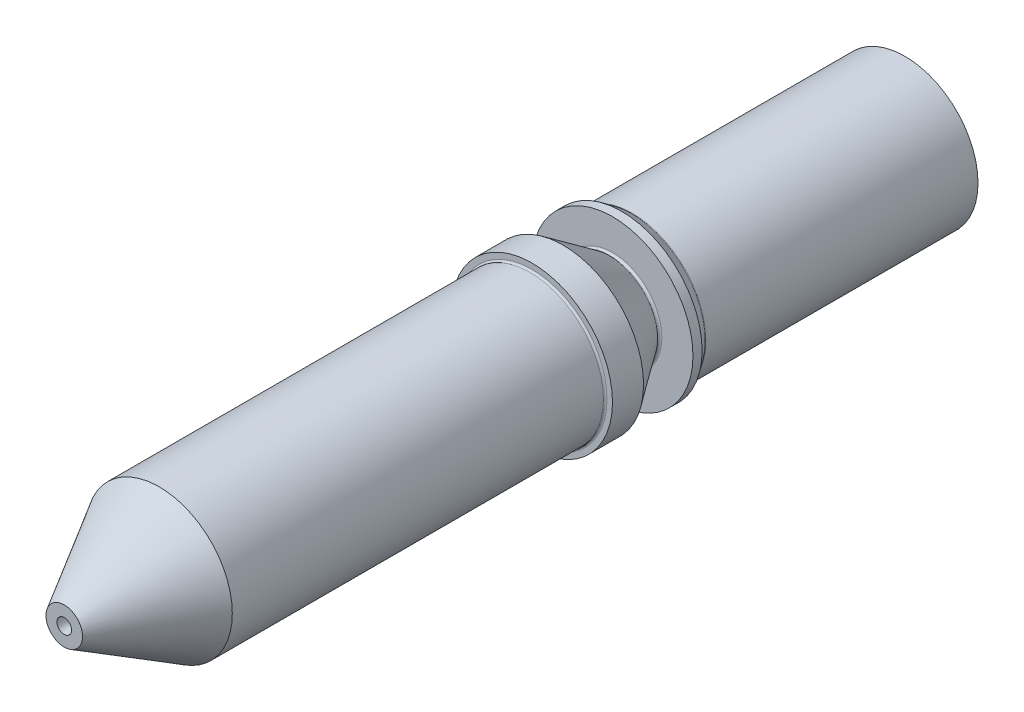
SolidWorks part; units mm, degrees
material "AISI Type 316L stainless steel"
ref_plane "Front Plane" through (0, 0, 0) normal (0, 0, 1) x (1, 0, 0)
ref_plane "Top Plane" through (0, 0, 0) normal (0, 1, 0) x (1, 0, 0)
ref_plane "Right Plane" through (0, 0, 0) normal (1, 0, 0) x (0, 0, -1)
sketch "Sketch1" plane through (0, 0, 0) normal (0, 1, 0) x (1, 0, 0)
  line L0 (0.5, -23) -> (2, -20.4019)
  line L1 (2, -20.4019) -> (2, -10.25)
  line L2 (0.5, -22.4197) -> (0.5, -21.8)
  line L3 (0.5, -21.8) -> (1, -21.4996)
  line L4 (2.2, -9.3498) -> (1.309, -8.0774)
  line L5 (1.35, -7.9987) -> (2.2, -7.9987)
  line L6 (2, -7.4473) -> (2, 0)
  line L7 (2.05, -10.2) -> (2.2, -10.2)
  line L8 (2.2, -10.2) -> (2.2, -9.3498)
  line L9 (2.009, -7.476) -> (2.2, -7.7487)
  line L10 (2.2, -7.7487) -> (2.2, -7.9987)
  line L11 (1, 0) -> (1, -21.4996)
  line L12 (0.5, -22.4197) -> (0.2, -22.6)
  line L13 (0.2, -22.6) -> (0.2, -23)
  line L14 (0.2, -23) -> (0.5, -23)
  line L15 (0, 0) -> (0, -33.6776) construction
  line L16 (1, 0) -> (2, 0)
  arc A0 (1.309, -8.0774) -> (1.35, -7.9987) centre (1.35, -8.0487) cw
  arc A1 (2, -10.25) -> (2.05, -10.2) centre (2.05, -10.25) cw
  arc A2 (2, -7.4473) -> (2.009, -7.476) centre (2.05, -7.4473) ccw
  point P9 (1.3, -8.0487)
  dimension "D10" = 0.05
  dimension "D17" = 0.25
  dimension "D2" = 4
  dimension "D3" = 31
  dimension "D4" = 1.2
  dimension "D5" = 0.4
  dimension "D6" = 60
  dimension "D7" = 1
  dimension "D8" = 15.0013
  dimension "D9" = 55
  dimension "D11" = 2.6
  dimension "D12" = 2
  dimension "D13" = 23
  dimension "D14" = 0.4
  dimension "D15" = 1
  dimension "D16" = 12.8
  dimension "D18" = 4.4
revolve "Revolve1" add sketch "Sketch1" angle 360 about L15
cosmetic thread "Cosmetic Thread1" parameters "D1"=11.8, "D2"=3.22
cosmetic thread "Cosmetic Thread2" parameters "D1"=7.5, "D2"=3.22
